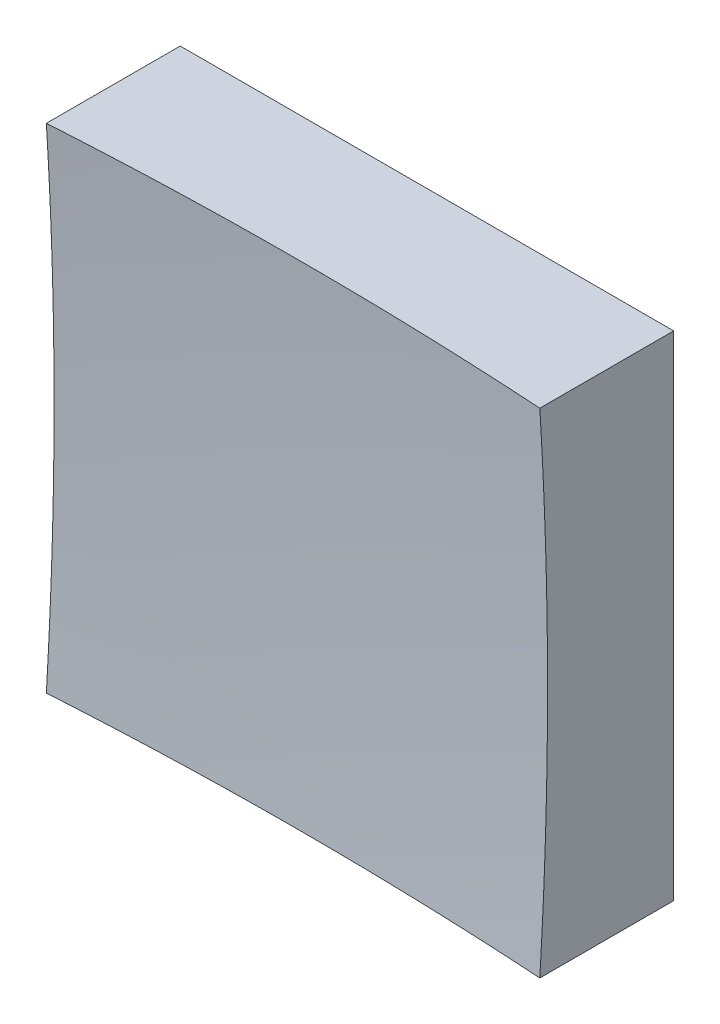
SolidWorks part; units mm, degrees
ref_plane "前视基准面" through (0, 0, 0) normal (0, 0, 1) x (1, 0, 0)
ref_plane "上视基准面" through (0, 0, 0) normal (0, 1, 0) x (1, 0, 0)
ref_plane "右视基准面" through (0, 0, 0) normal (1, 0, 0) x (0, 0, -1)
sketch "草图1" plane through (0, 0, 0) normal (0, 0, 1) x (1, 0, 0)
  line L1 (-12.5, 12.5) -> (12.5, 12.5)
  line L2 (-12.5, 12.5) -> (-12.5, -12.5)
  line L3 (-12.5, -12.5) -> (12.5, -12.5)
  line L4 (12.5, 12.5) -> (12.5, -12.5)
  line L5 (-12.5, 12.5) -> (12.5, -12.5) construction
  line L6 (-12.5, -12.5) -> (12.5, 12.5) construction
  point P0 (0, 0)
  dimension "D1" = 25
  dimension "D2" = 25
extrude "凸台-拉伸1" add sketch "草图1" along normal blind 20 contours L2 L3 L4 L1
sketch "草图2" plane through (0, 0, 0) normal (0, 1, 0) x (1, 0, 0)
  line L0 (-7.4603, -6) -> (7.3192, -6) construction
  line L1 (0, 0) -> (0, -12.1749) construction
  line L2 (194.9691, -161.4236) -> (0, -161.4236)
  line L3 (0, -161.4236) -> (0, -6)
  arc A1 (194.9691, -161.4236) -> (0, -6) centre (0, -206) ccw
  dimension "D2" = 400
  dimension "D1" = 6
revolve "切除-旋转2" cut sketch "草图2" angle 360 about L3
